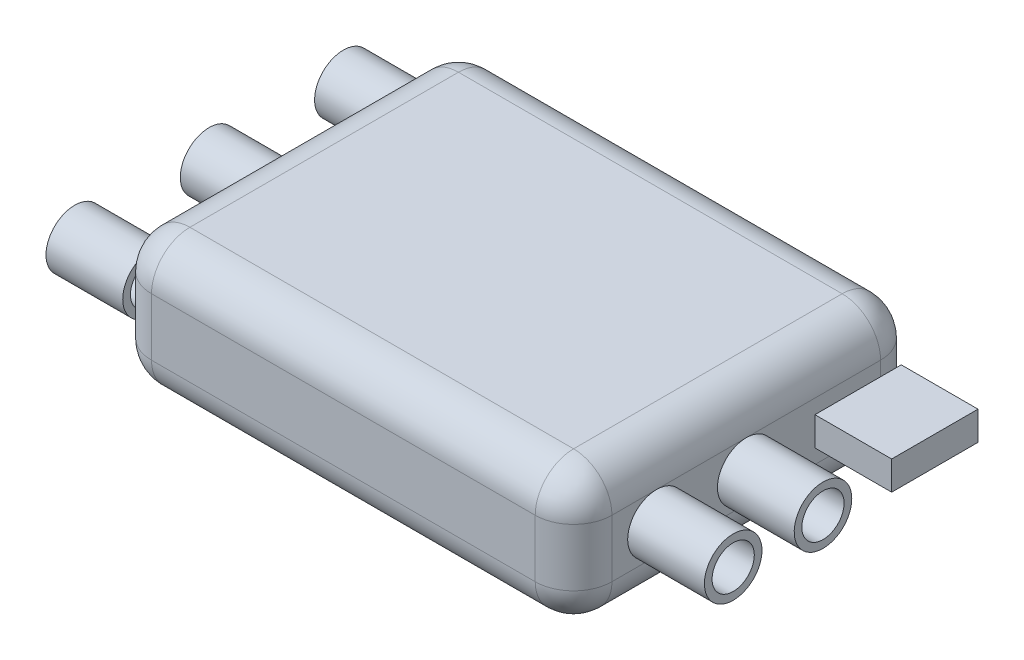
SolidWorks part; units mm, degrees
ref_plane "Front Plane" through (0, 0, 0) normal (0, 0, 1) x (1, 0, 0)
ref_plane "Top Plane" through (0, 0, 0) normal (0, 1, 0) x (1, 0, 0)
ref_plane "Right Plane" through (0, 0, 0) normal (1, 0, 0) x (0, 0, -1)
sketch "Sketch1" plane through (0, 0, 0) normal (0, 1, 0) x (1, 0, 0)
  line L1 (10, -9) -> (-10, -9)
  line L2 (12, -7) -> (12, 7)
  line L3 (10, 9) -> (-10, 9)
  line L4 (-12, -7) -> (-12, 7)
  line L5 (12, -9) -> (-12, 9) construction
  line L6 (12, 9) -> (-12, -9) construction
  arc A0 (-10, -9) -> (-12, -7) centre (-10, -7) cw
  arc A1 (10, -9) -> (12, -7) centre (10, -7) ccw
  arc A2 (12, 7) -> (10, 9) centre (10, 7) ccw
  arc A3 (-10, 9) -> (-12, 7) centre (-10, 7) ccw
  point P0 (0, 0)
  dimension "D3" = 2
  dimension "D1" = 24
  dimension "D2" = 18
extrude "Boss-Extrude1" add sketch "Sketch1" along normal blind 7
fillet "Fillet1" radius 2 16 edges at (0, 0, 9) (11.4142, 0, 8.4142) (12, 0, 0) (11.4142, 0, -8.4142) (0, 0, -9) (-11.4142, 0, -8.4142) (-12, 0, 0) (-11.4142, 0, 8.4142) (-12, 7, 0) (-11.4142, 7, -8.4142) (0, 7, -9) (11.4142, 7, -8.4142) (12, 7, 0) (11.4142, 7, 8.4142) (0, 7, 9) (-11.4142, 7, 8.4142)
sketch "Sketch3" plane through (-12, 0, 0) normal (-1, 0, 0) x (0, 0, 1)
  line L0 (-7, 3.5) -> (7, 3.5) construction
  line L1 (-7, 5) -> (-7, 2) construction
  line L2 (7, 5) -> (7, 2) construction
  circle A0 centre (7, 3.5) radius 1.5
  circle A1 centre (0, 3.5) radius 1.5
  circle A2 centre (-7, 3.5) radius 1.5
  circle A3 centre (-7, 3.5) radius 1.1
  circle A4 centre (0, 3.5) radius 1.1
  circle A5 centre (7, 3.5) radius 1.1
  dimension "D1" = 0.4
  dimension "D2" = 3
extrude "Boss-Extrude2" add sketch "Sketch3" along normal blind 4
sketch "Sketch4" plane through (12, 0, 0) normal (1, 0, 0) x (0, 0, -1)
  line L0 (-7, 3.5) -> (7, 3.5) construction
  line L1 (-7, 5) -> (-7, 2) construction
  line L2 (7, 5) -> (7, 2) construction
  line L4 (3.5803, 2.75) -> (8.0803, 2.75)
  line L5 (3.5803, 2.75) -> (3.5803, 4.25)
  line L6 (3.5803, 4.25) -> (8.0803, 4.25)
  line L7 (8.0803, 2.75) -> (8.0803, 4.25)
  line L8 (3.5803, 2.75) -> (8.0803, 4.25) construction
  line L9 (3.5803, 4.25) -> (8.0803, 2.75) construction
  circle A0 centre (-4.6804, 3.5) radius 1.5
  circle A1 centre (-4.6804, 3.5) radius 1.1
  circle A2 centre (0, 3.5) radius 1.5
  circle A3 centre (0, 3.5) radius 1.1
  point P6 (5.8303, 3.5)
  dimension "D3" = 3
  dimension "D4" = 0.4
  dimension "D1" = 4.5
  dimension "D2" = 1.5
extrude "Boss-Extrude3" add sketch "Sketch4" along normal blind 4
